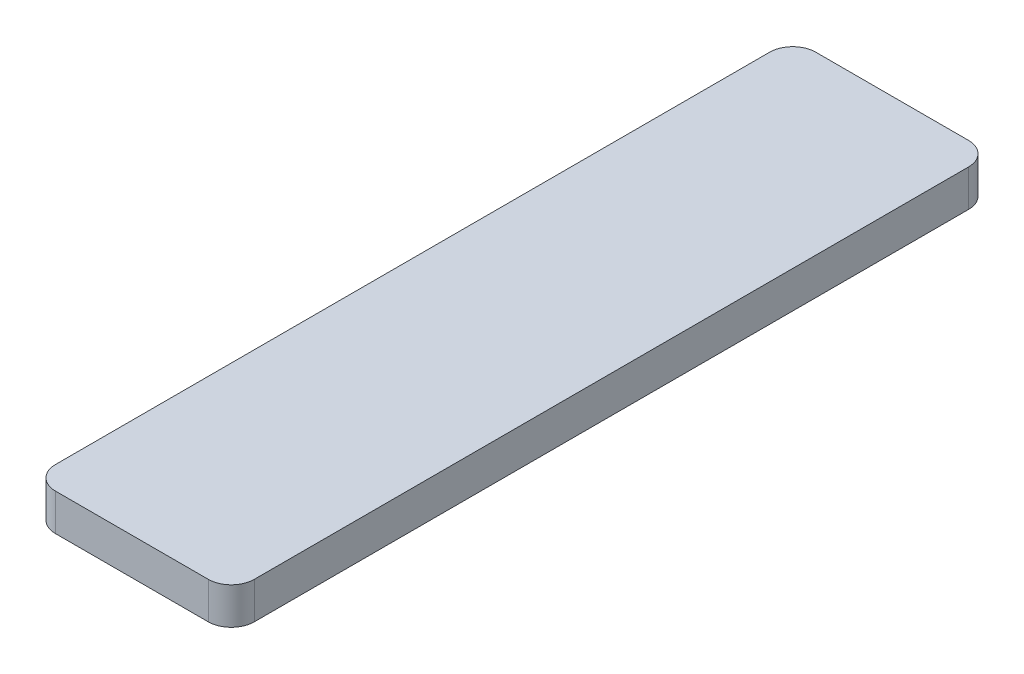
SolidWorks part; units mm, degrees
ref_plane "Front Plane" through (0, 0, 0) normal (0, 0, 1) x (1, 0, 0)
ref_plane "Top Plane" through (0, 0, 0) normal (0, 1, 0) x (1, 0, 0)
ref_plane "Right Plane" through (0, 0, 0) normal (1, 0, 0) x (0, 0, -1)
sketch "Sketch2" plane through (0, 0, 0) normal (0, 1, 0) x (1, 0, 0)
  line L0 (-104.5149, -49.0671) -> (-104.5149, -16.0471)
  line L1 (-104.5149, -16.0471) -> (-95.8789, -16.0471)
  line L2 (-95.8789, -16.0471) -> (-95.8789, -49.0671)
  line L14 (-104.5149, -49.0671) -> (-95.8789, -49.0671)
  point P0 (-100.1969, -49.0671)
extrude "Boss-Extrude1" add sketch "Sketch2" along normal blind 1.6
fillet "Fillet1" radius 1 4 edges at (-104.5149, 0.8, 16.0471) (-95.8789, 0.8, 16.0471) (-95.8789, 0.8, 49.0671) (-104.5149, 0.8, 49.0671)
